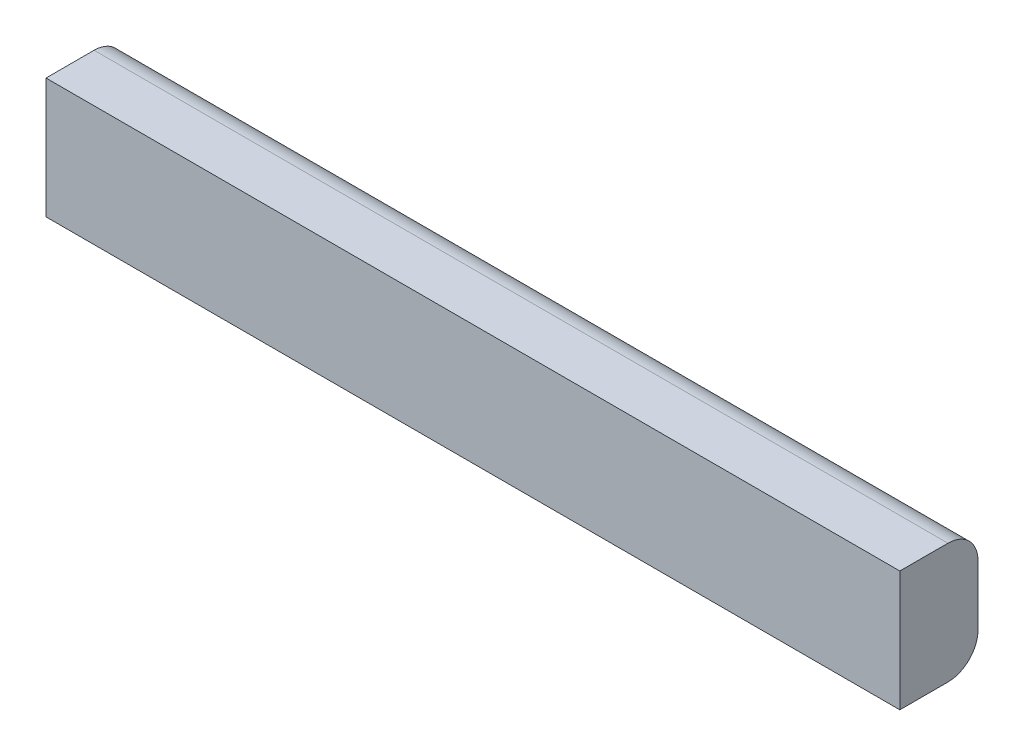
SolidWorks part; units mm, degrees
ref_plane "Front Plane" through (0, 0, 0) normal (0, 0, 1) x (1, 0, 0)
ref_plane "Top Plane" through (0, 0, 0) normal (0, 1, 0) x (1, 0, 0)
ref_plane "Right Plane" through (0, 0, 0) normal (1, 0, 0) x (0, 0, -1)
sketch "Sketch1" plane through (0, 0, 0) normal (1, 0, 0) x (0, 0, -1)
  line L1 (49.3736, 66.0217) -> (-1.4264, 66.0217)
  line L2 (81.1236, 34.2717) -> (81.1236, -29.2283)
  line L3 (49.3736, -60.9783) -> (-1.4264, -60.9783)
  line L4 (-1.4264, 66.0217) -> (-1.4264, -60.9783)
  arc A0 (49.3736, 66.0217) -> (81.1236, 34.2717) centre (49.3736, 34.2717) cw
  arc A1 (81.1236, -29.2283) -> (49.3736, -60.9783) centre (49.3736, -29.2283) cw
  point P8 (81.1236, -60.9783)
  dimension "D3" = 31.75
  dimension "D1" = 127
  dimension "D2" = 82.55
extrude "Boss-Extrude1" add sketch "Sketch1" along normal mid plane 901.7
equation "\"bumple\"= 24in'bumpler length"
equation "\"D1@Boss-Extrude1\"=\"bumple\""
